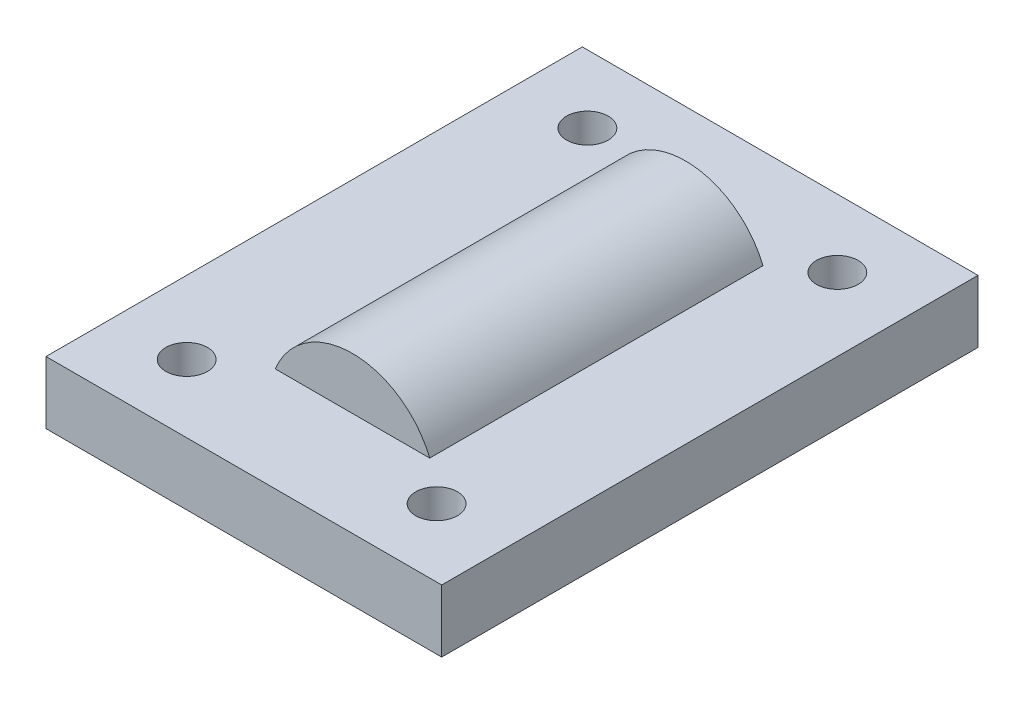
SolidWorks part; units mm, degrees
ref_plane "Alzado" through (0, 0, 0) normal (0, 0, 1) x (1, 0, 0)
ref_plane "Planta" through (0, 0, 0) normal (0, 1, 0) x (1, 0, 0)
ref_plane "Vista lateral" through (0, 0, 0) normal (1, 0, 0) x (0, 0, -1)
sketch "Croquis1" plane through (0, 0, 0) normal (0, 1, 0) x (1, 0, 0)
  line L0 (9.2731, 12.7615) -> (-9.7269, 12.7615)
  line L5 (-9.7269, 12.7615) -> (-9.7269, -12.9885)
  line L6 (-9.7269, -12.9885) -> (9.2731, -12.9885)
  line L7 (9.2731, -12.9885) -> (9.2731, 12.7615)
  circle A0 centre (-6.2269, 9.5065) radius 1
  circle A1 centre (5.7731, 9.5065) radius 1
  circle A2 centre (5.7731, -9.7335) radius 1
  circle A3 centre (-6.2269, -9.7335) radius 1
extrude "Saliente-Extruir1" add sketch "Croquis1" along normal blind 3
sketch "Croquis2" plane through (0, 0, 0) normal (0, 0, 1) x (1, 0, 0)
  line L0 (-3.7081, 3) -> (3.7081, 3)
  line L1 (-9.7269, 3) -> (9.2731, 3) construction
  arc A0 (3.7081, 3) -> (-3.7081, 3) centre (0, 1.5) ccw
  dimension "D1" = 8
  dimension "D2" = 1.5
extrude "Saliente-Extruir2" add sketch "Croquis2" along normal blind 8 and the other way blind 8
